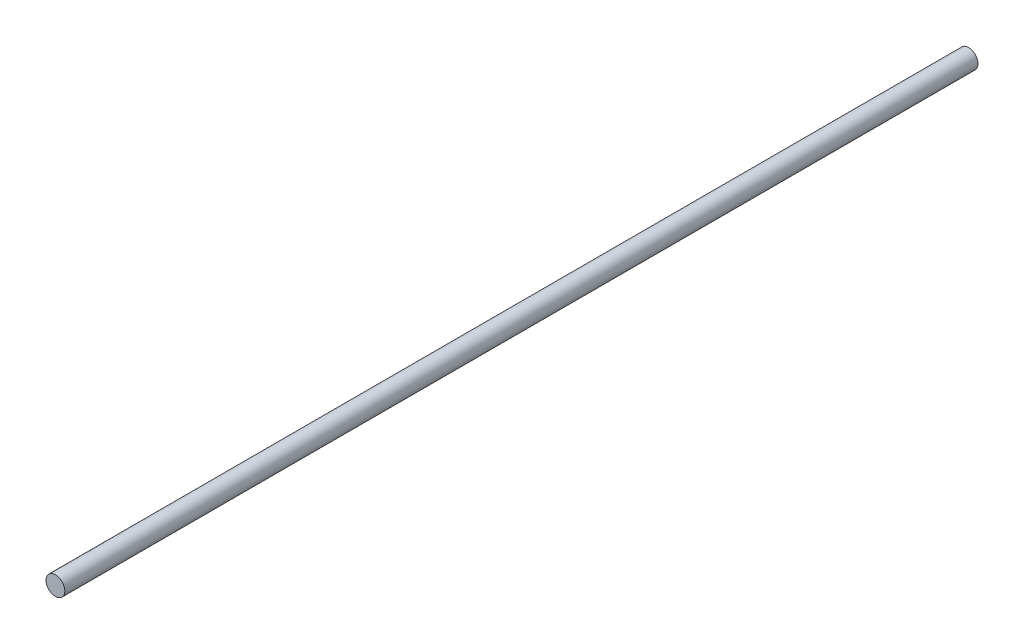
SolidWorks part; units mm, degrees
ref_plane "前视基准面" through (0, 0, 0) normal (0, 0, 1) x (1, 0, 0)
ref_plane "上视基准面" through (0, 0, 0) normal (0, 1, 0) x (1, 0, 0)
ref_plane "右视基准面" through (0, 0, 0) normal (1, 0, 0) x (0, 0, -1)
sketch "草图1" plane through (0, 0, 0) normal (0, 0, 1) x (1, 0, 0)
  circle A0 centre (0, 0) radius 3
  dimension "D1" = 6
extrude "凸台-拉伸1" add sketch "草图1" along normal blind 291.2
